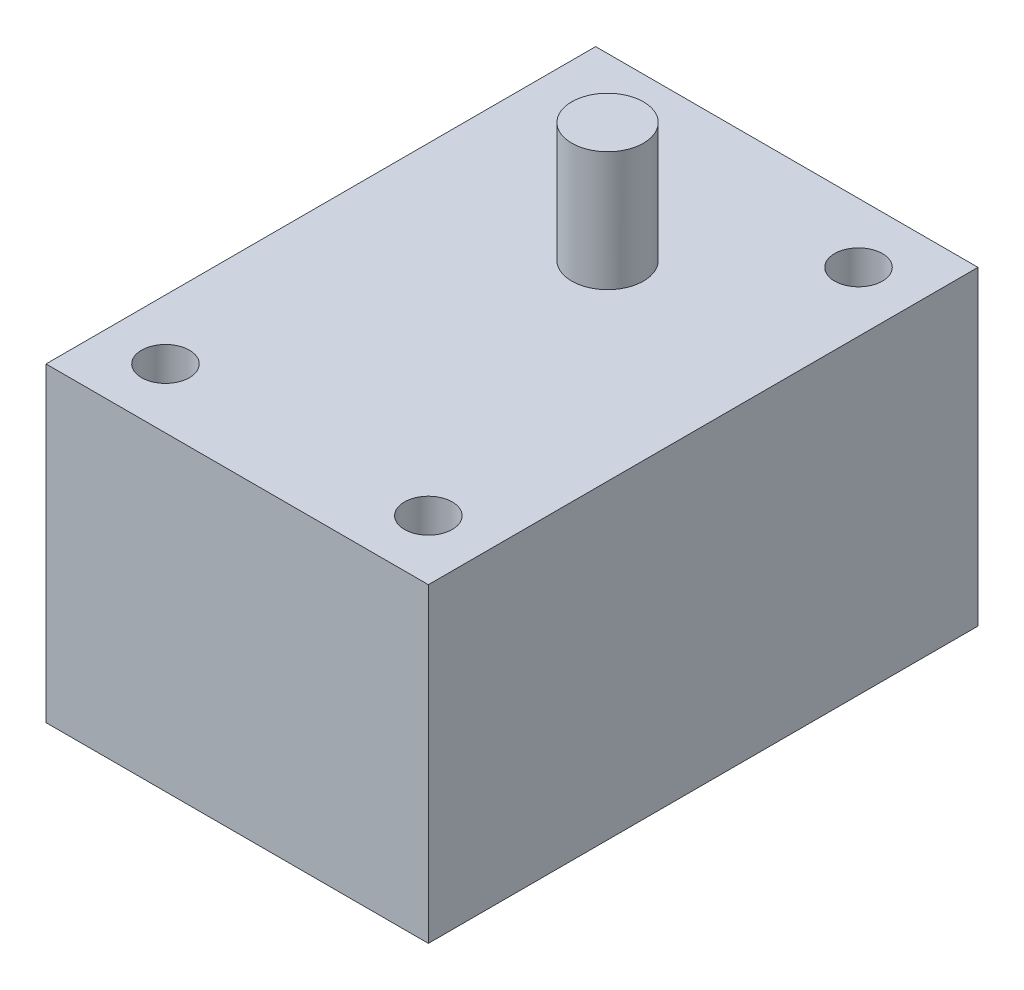
SolidWorks part; units mm, degrees
material "6061 Alloy"
ref_plane "Front Plane" through (0, 0, 0) normal (0, 0, 1) x (1, 0, 0)
ref_plane "Top Plane" through (0, 0, 0) normal (0, 1, 0) x (1, 0, 0)
ref_plane "Right Plane" through (0, 0, 0) normal (1, 0, 0) x (0, 0, -1)
sketch "Sketch2" plane through (0, 0, 0) normal (0, 0, 1) x (1, 0, 0)
  line L1 (0, 0) -> (32, 0)
  line L2 (0, 0) -> (0, 26)
  line L3 (0, 26) -> (32, 26)
  line L4 (32, 0) -> (32, 26)
  dimension "D1" = 26
  dimension "D2" = 32
extrude "base" add sketch "Sketch2" along normal blind 46
sketch "Sketch3" plane through (0, 26, 0) normal (0, 1, 0) x (1, 0, 0)
  line L12 (27, -5) -> (5, -5)
  line L13 (5, -5) -> (5, -41)
  line L14 (5, -41) -> (27, -41)
  line L15 (27, -41) -> (27, -5)
  line L16 (27, -5) -> (5, -5) construction
  line L17 (5, -5) -> (5, -41) construction
  line L18 (5, -41) -> (27, -41) construction
  line L19 (27, -41) -> (27, -5) construction
  circle A0 centre (5, -5) radius 2
  circle A1 centre (27, -5) radius 2
  circle A2 centre (27, -41) radius 2
  circle A3 centre (5, -41) radius 2
  dimension "D2" = 4
  dimension "D1" = 5
extrude "mounting holes" cut sketch "Sketch3" against normal blind 10
sketch "Sketch4" plane through (0, 26, 0) normal (0, 1, 0) x (1, 0, 0)
  line L4 (32, 0) -> (0, 0)
  line L5 (0, 0) -> (0, -46)
  line L6 (0, -46) -> (32, -46)
  line L7 (32, -46) -> (32, 0)
  line L8 (32, 0) -> (0, 0)
  line L9 (0, 0) -> (0, -46)
  line L10 (0, -46) -> (32, -46)
  line L11 (32, -46) -> (32, 0)
  circle A0 centre (16, -15) radius 3
  point P4 (16, 0)
  dimension "D2" = 6
  dimension "D3" = 15
  dimension "D1" = 0
extrude "axle" add sketch "Sketch4" along normal blind 10 contours A0
